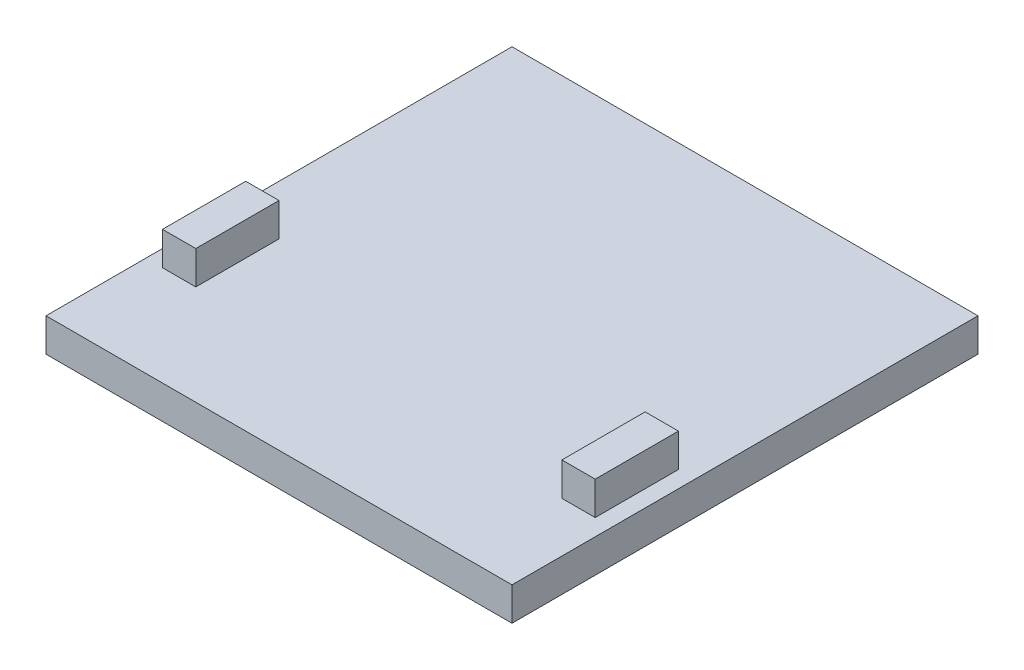
SolidWorks part; units mm, degrees
ref_plane "Front Plane" through (0, 0, 0) normal (0, 0, 1) x (1, 0, 0)
ref_plane "Top Plane" through (0, 0, 0) normal (0, 1, 0) x (1, 0, 0)
ref_plane "Right Plane" through (0, 0, 0) normal (1, 0, 0) x (0, 0, -1)
sketch "Sketch1" plane through (0, 0, 0) normal (0, 1, 0) x (1, 0, 0)
  line L1 (-355.6, -355.6) -> (355.6, -355.6)
  line L2 (-355.6, -355.6) -> (-355.6, 355.6)
  line L3 (-355.6, 355.6) -> (355.6, 355.6)
  line L4 (355.6, -355.6) -> (355.6, 355.6)
  line L5 (-355.6, -355.6) -> (355.6, 355.6) construction
  line L6 (-355.6, 355.6) -> (355.6, -355.6) construction
  point P0 (0, 0)
  dimension "D1" = 711.2
  dimension "D2" = 711.2
extrude "Boss-Extrude1" add sketch "Sketch1" along normal blind 50.8
sketch "Sketch2" plane through (0, 50.8, 0) normal (0, 1, 0) x (1, 0, 0)
  line L0 (355.6, -355.6) -> (355.6, 355.6) construction
  line L1 (330.2, -203.2) -> (279.4, -203.2)
  line L2 (330.2, -203.2) -> (330.2, -76.2)
  line L3 (330.2, -76.2) -> (279.4, -76.2)
  line L4 (279.4, -203.2) -> (279.4, -76.2)
  line L5 (0, -355.6) -> (0, 355.6) construction
  line L6 (-355.6, -355.6) -> (355.6, -355.6) construction
  line L7 (355.6, 355.6) -> (-355.6, 355.6) construction
  line L8 (-330.2, -203.2) -> (-330.2, -76.2)
  line L9 (-330.2, -203.2) -> (-279.4, -203.2)
  line L10 (-279.4, -203.2) -> (-279.4, -76.2)
  line L11 (-330.2, -76.2) -> (-279.4, -76.2)
  dimension "D1" = 50.8
  dimension "D2" = 127
  dimension "D3" = 25.4
  dimension "D4" = 152.4
extrude "Boss-Extrude2" add sketch "Sketch2" along normal blind 50.8
